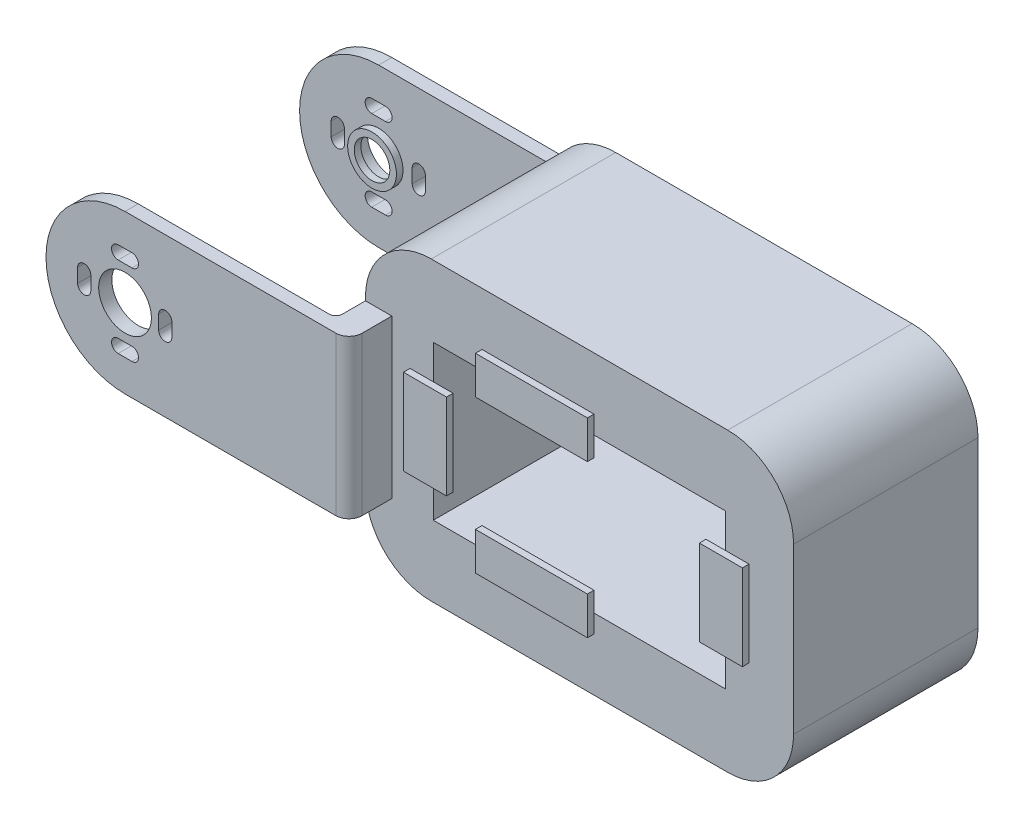
SolidWorks part; units mm, degrees
ref_plane "前基準面" through (0, 0, 0) normal (0, 0, 1) x (1, 0, 0)
ref_plane "上基準面" through (0, 0, 0) normal (0, 1, 0) x (1, 0, 0)
ref_plane "右基準面" through (0, 0, 0) normal (1, 0, 0) x (0, 0, -1)
sketch "草圖1" plane through (0, 0, 0) normal (0, 0, 1) x (1, 0, 0)
  line L0 (-9.02, 0) -> (7.9922, 0) construction
  line L2 (-59.9347, 22.5) -> (5.0653, 22.5)
  line L3 (-59.9347, 22.5) -> (-59.9347, -22.5)
  line L4 (-59.9347, -22.5) -> (5.0653, -22.5)
  line L5 (5.0653, 22.5) -> (5.0653, -22.5)
  dimension "D1" = 45
  dimension "D2" = 22.5
  dimension "D3" = 65
extrude "填料-伸長1" add sketch "草圖1" along normal blind 28
sketch "草圖2" plane through (0, 0, 0) normal (0, 0, 1) x (1, 0, 0)
  line L0 (-59.9347, 0) -> (5.361, 0) construction
  line L1 (-59.9347, 22.5) -> (-59.9347, -22.5) construction
  line L2 (-27.4347, 22.5) -> (-27.4347, -22.5) construction
  line L3 (5.0653, 22.5) -> (-59.9347, 22.5) construction
  line L4 (-59.9347, -22.5) -> (5.0653, -22.5) construction
  line L6 (-49.6347, 11.7) -> (-5.2347, 11.7)
  line L7 (-49.6347, 11.7) -> (-49.6347, -11.7)
  line L8 (-49.6347, -11.7) -> (-5.2347, -11.7)
  line L9 (-5.2347, 11.7) -> (-5.2347, -11.7)
  dimension "D1" = 44.4
  dimension "D2" = 23.4
  dimension "D3" = 10.3
  dimension "D4" = 10.8
extrude "除料-伸長1" cut sketch "草圖2" along normal blind 39
ref_plane "平面1" through (0, 0, 28) normal (0, 0, 1) x (1, 0, 0)
sketch "草圖3" plane through (0, 0, 28) normal (0, 0, 1) x (1, 0, 0)
  line L0 (-59.9347, 22.5) -> (-59.9347, -22.5) construction
  line L2 (-59.9347, 12) -> (-55.9347, 12)
  line L3 (-59.9347, 12) -> (-59.9347, -12)
  line L4 (-59.9347, -12) -> (-55.9347, -12)
  line L5 (-55.9347, 12) -> (-55.9347, -12)
  line L8 (-5.2347, -11.7) -> (-49.6347, -11.7) construction
  dimension "D1" = 4
  dimension "D2" = 24
  dimension "D3" = 0.3
extrude "填料-伸長2" add sketch "草圖3" along normal blind 6
ref_plane "平面2" through (-59.9347, 0, 0) normal (-1, 0, 0) x (0, 0, 1)
sketch "草圖4" plane through (-59.9347, 0, 0) normal (-1, 0, 0) x (0, 0, 1)
  line L0 (34, 12) -> (28, 12) construction
  line L2 (32, 12) -> (34, 12)
  line L3 (32, 12) -> (32, -12)
  line L4 (32, -12) -> (34, -12)
  line L5 (34, 12) -> (34, -12)
  dimension "D1" = 2
ref_plane "平面3" through (0, 0, 33) normal (0, 0, 1) x (1, 0, 0)
sketch "草圖6" plane through (0, 0, 28) normal (0, 0, 1) x (1, 0, 0)
  line L0 (-15.2347, 0.3) -> (5.0653, -22.5)
  line L1 (-5.2347, 11.7) -> (-5.2347, -11.7) construction
  line L2 (-5.2347, -11.7) -> (-49.6347, -11.7) construction
  line L3 (-15.2347, 0.3) -> (-15.2347, -22.5)
  line L4 (-59.9347, -22.5) -> (5.0653, -22.5) construction
  line L5 (-15.2347, -22.5) -> (5.0653, -22.5)
  dimension "D1" = 10
  dimension "D2" = 12
sketch "草圖7" plane through (0, 0, 33) normal (0, 0, 1) x (1, 0, 0)
  line L1 (-59.9347, 12) -> (-59.9347, -12) construction
  line L3 (-59.9347, 0) -> (-109.9347, 0) construction
  line L5 (-96.1347, 1.05) -> (-96.1347, -1.05) construction
  line L6 (-95.1347, 1.05) -> (-95.1347, -1.05)
  line L7 (-97.1347, 1.05) -> (-97.1347, -1.05)
  line L8 (-90.9847, -6.2) -> (-88.8847, -6.2) construction
  line L9 (-90.9847, -5.2) -> (-88.8847, -5.2)
  line L10 (-90.9847, -7.2) -> (-88.8847, -7.2)
  line L11 (-89.9347, 4) -> (-89.9347, -7.9506) construction
  line L12 (-90.9847, 6.1) -> (-88.8847, 6.1) construction
  line L13 (-90.9847, 5.1) -> (-88.8847, 5.1)
  line L14 (-90.9847, 7.1) -> (-88.8847, 7.1)
  line L15 (-83.8347, 1.05) -> (-83.8347, -1.05) construction
  line L16 (-84.8347, 1.05) -> (-84.8347, -1.05)
  line L17 (-82.8347, 1.05) -> (-82.8347, -1.05)
  line L19 (-59.9347, 12) -> (-59.9347, -12)
  line L20 (-59.9347, -12) -> (-89.9347, -12)
  line L21 (-59.9347, 12) -> (-89.9347, 12)
  circle A1 centre (-89.9347, 0) radius 4
  arc A3 (-95.1347, 1.05) -> (-97.1347, 1.05) centre (-96.1347, 1.05) ccw
  arc A4 (-97.1347, -1.05) -> (-95.1347, -1.05) centre (-96.1347, -1.05) ccw
  arc A5 (-90.9847, -5.2) -> (-90.9847, -7.2) centre (-90.9847, -6.2) ccw
  arc A6 (-88.8847, -7.2) -> (-88.8847, -5.2) centre (-88.8847, -6.2) ccw
  arc A7 (-90.9847, 5.1) -> (-90.9847, 7.1) centre (-90.9847, 6.1) cw
  arc A8 (-88.8847, 7.1) -> (-88.8847, 5.1) centre (-88.8847, 6.1) cw
  arc A9 (-84.8347, 1.05) -> (-82.8347, 1.05) centre (-83.8347, 1.05) cw
  arc A10 (-82.8347, -1.05) -> (-84.8347, -1.05) centre (-83.8347, -1.05) cw
  arc A11 (-89.9347, 12) -> (-89.9347, -12) centre (-89.9347, 0) ccw
  point P15 (-96.1347, 0)
  point P20 (-89.9347, -6.2)
  point P31 (-89.9347, 6.1)
  point P38 (-83.8347, 0)
  dimension "D2" = 8
  dimension "D3" = 50
  dimension "D4" = 6.2
  dimension "D6" = 0
  dimension "D12" = 24
  dimension "D5" = 2.1
  dimension "D7" = 2
  dimension "D8" = 2
  dimension "D9" = 0
  dimension "D10" = 2.1
  dimension "D11" = 6.2
  dimension "D13" = 30
extrude "填料-伸長3" add sketch "草圖7" along normal blind 1.5 and the other way blind 0.5
ref_plane "平面4" through (0, 0, 0) normal (0, 0, -1) x (-1, 0, 0)
sketch "草圖8" plane through (0, 0, 0) normal (0, 0, -1) x (-1, 0, 0)
  line L0 (59.9347, 12) -> (59.9347, -12) construction
  line L1 (55.9347, 12) -> (59.9347, 12)
  line L2 (55.9347, 12) -> (55.9347, -12)
  line L3 (55.9347, -12) -> (59.9347, -12)
  line L4 (59.9347, 12) -> (59.9347, -12)
  dimension "D1" = 24
  dimension "D2" = 4
extrude "填料-伸長4" add sketch "草圖8" along normal blind 6 contours L3 L4 L1 L2
fillet "圓角1" radius 10 1 edges at (-59.9347, -22.5, 14)
fillet "圓角2" radius 10 1 edges at (-59.9347, 22.5, 14)
fillet "圓角3" radius 10 1 edges at (5.0653, 22.5, 14)
fillet "圓角4" radius 10 1 edges at (5.0653, -22.5, 14)
pattern_linear "直線複製排列2" count 2 spacing 38.5 along (0, 0, -1) of "填料-伸長3"
fillet "圓角5" radius 2 1 edges at (-55.9347, 0, -6)
ref_plane "平面5" through (0, 0, -4) normal (0, 0, 1) x (1, 0, 0)
sketch "草圖9" plane through (0, 0, -4) normal (0, 0, 1) x (1, 0, 0)
  circle A0 centre (-89.9347, 0) radius 3.7
  circle A1 centre (-89.9347, 0) radius 2.7
  dimension "D1" = 7.4
  dimension "D2" = 5.4
extrude "填料-伸長5" add sketch "草圖9" along normal blind 1 separate body
ref_plane "平面6" through (0, 0, 29) normal (0, 0, 1) x (1, 0, 0)
sketch "草圖10" plane through (0, 0, 29) normal (0, 0, 1) x (1, 0, 0)
  line L6 (-49.6347, 0) -> (-4.2092, 0) construction
  line L7 (-49.6347, -11.7) -> (-49.6347, 11.7) construction
  line L8 (-27.4347, -11.7) -> (-27.4347, 19.297) construction
  line L9 (-5.2347, -11.7) -> (-49.6347, -11.7) construction
  line L11 (-49.6347, 6.5) -> (-53.1651, 6.5)
  line L14 (-53.1651, 6.5) -> (-53.1651, -6.5)
  line L17 (-49.6347, 6.5) -> (-46.6347, 6.5)
  line L18 (-46.6347, 6.5) -> (-46.6347, -6.5)
  line L20 (-42.2347, -11.7) -> (-42.2347, -8.7)
  line L25 (-42.2347, -11.7) -> (-42.2347, -14.4546)
  line L27 (-8.2347, 6.5) -> (-8.2347, -6.5)
  line L28 (-8.2347, -6.5) -> (-5.2347, -6.5)
  line L29 (-5.2347, -6.5) -> (-1.7043, -6.5)
  line L30 (-1.7043, 6.5) -> (-1.7043, -6.5)
  line L32 (-25.2347, 8.7) -> (-25.2347, 14.4546)
  line L33 (-25.2347, -14.4546) -> (-25.2347, -8.7)
  line L34 (-25.2347, -14.4546) -> (-42.2347, -14.4546)
  line L35 (-25.2347, -8.7) -> (-42.2347, -8.7)
  line L36 (-25.2347, 8.7) -> (-42.2347, 8.7)
  line L37 (-25.2347, 14.4546) -> (-42.2347, 14.4546)
  line L38 (-42.2347, 8.7) -> (-42.2347, 14.4546)
  line L39 (-46.6347, -6.5) -> (-53.1651, -6.5)
  line L40 (-1.7043, 6.5) -> (-8.2347, 6.5)
  dimension "D3" = 13
  dimension "D4" = 6.5
extrude "填料-伸長6" add sketch "草圖10" against normal blind 1 separate body
ref_plane "平面7" through (0, 0, -4) normal (0, 0, -1) x (-1, 0, 0)
sketch "草圖12" plane through (0, 0, -4) normal (0, 0, -1) x (-1, 0, 0)
  circle A0 centre (89.9347, 0) radius 4
  circle A1 centre (89.9347, 0) radius 3.7
extrude "填料-伸長8" add sketch "草圖12" along normal blind 2
ref_plane "平面9" through (0, 0, 34) normal (0, 0, 1) x (1, 0, 0)
sketch "草圖15" plane through (0, 0, 34) normal (0, 0, 1) x (1, 0, 0)
  line L0 (-59.9347, 12) -> (-59.9347, -12) construction
  line L1 (-59.9347, 12) -> (-55.9347, 12)
  line L2 (-59.9347, 12) -> (-59.9347, -12)
  line L3 (-59.9347, -12) -> (-55.9347, -12)
  line L4 (-55.9347, 12) -> (-55.9347, -12)
  line L5 (-55.9347, 12) -> (-59.9347, 12) construction
  dimension "D1" = 24
  dimension "D2" = 4
extrude "填料-伸長10" add sketch "草圖15" along normal blind 0.5
fillet "圓角16" radius 2 1 edges at (-55.9347, 0, 34.5)
fillet "圓角17" radius 1 1 edges at (-59.9347, 0, 32.5)
fillet "圓角18" radius 1 1 edges at (-59.9347, 0, -4)
